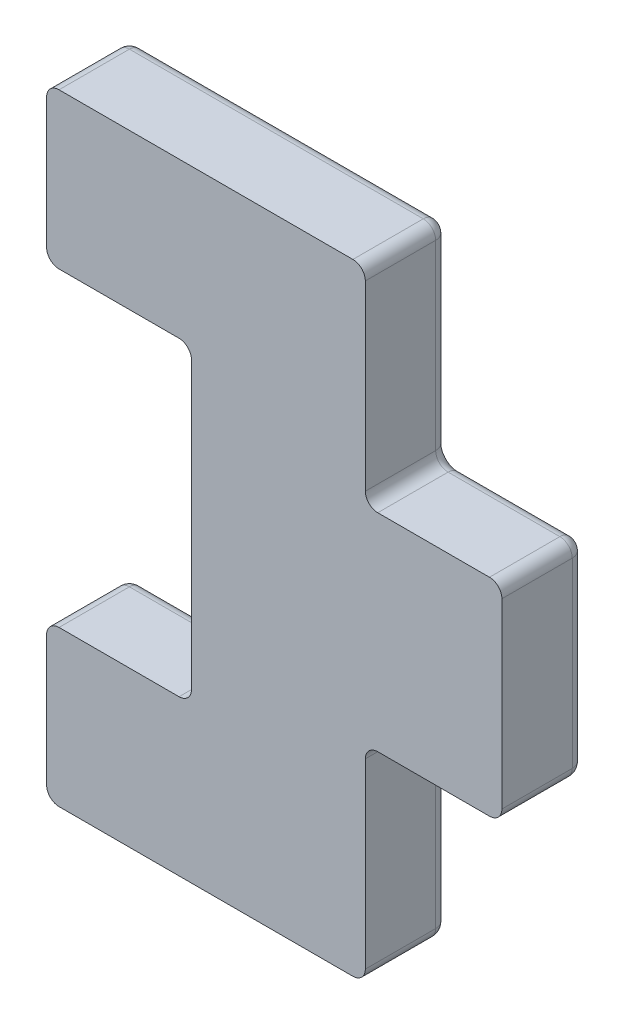
SolidWorks part; units mm, degrees
ref_plane "Ebene vorne" through (0, 0, 0) normal (0, 0, 1) x (1, 0, 0)
ref_plane "Ebene oben" through (0, 0, 0) normal (0, 1, 0) x (1, 0, 0)
ref_plane "Ebene rechts" through (0, 0, 0) normal (1, 0, 0) x (0, 0, -1)
sketch "Skizze1" plane through (0, 0, 0) normal (0, 0, 1) x (1, 0, 0)
  line L0 (0, 0) -> (7.5, 0) construction
  line L1 (0, -3.75) -> (0, 3.75)
  line L2 (0, 3.75) -> (-3.5, 3.75)
  line L3 (-3.5, 3.75) -> (-3.5, 7.5)
  line L4 (-3.5, 7.5) -> (4.2, 7.5)
  line L5 (4.2, 7.5) -> (4.2, 2.5)
  line L6 (4.2, 2.5) -> (7.5, 2.5)
  line L7 (7.5, 2.5) -> (7.5, -2.5)
  line L8 (4.2, -2.5) -> (7.5, -2.5)
  line L9 (4.2, -7.5) -> (4.2, -2.5)
  line L10 (-3.5, -7.5) -> (4.2, -7.5)
  line L11 (-3.5, -3.75) -> (-3.5, -7.5)
  line L12 (0, -3.75) -> (-3.5, -3.75)
  dimension "D1" = 15
  dimension "D2" = 7.5
  dimension "D3" = 5
  dimension "D4" = 11
  dimension "D5" = 7.7
  dimension "D6" = 3.5
extrude "Grundkörper" add sketch "Skizze1" along normal blind 2
fillet "Verrundung1" radius 0.3 12 edges at (4.2, 7.5, 1) (4.2, 2.5, 1) (7.5, 2.5, 1) (-3.5, 7.5, 1) (-3.5, 3.75, 1) (0, 3.75, 1) (0, -3.75, 1) (-3.5, -3.75, 1) (-3.5, -7.5, 1) (4.2, -7.5, 1) (4.2, -2.5, 1) (7.5, -2.5, 1)
fillet "Verrundung2" radius 0.3 24 edges at (-3.4121, 7.4121, 0) (-3.5, 5.625, 0) (-3.4121, 3.8379, 0) (-1.75, 3.75, 0) (-0.0879, 3.6621, 0) (0, 0, 0) (-0.0879, -3.6621, 0) (-1.75, -3.75, 0) (-3.4121, -3.8379, 0) (-3.5, -5.625, 0) (-3.4121, -7.4121, 0) (0.35, -7.5, 0) (4.1121, -7.4121, 0) (4.2, -5, 0) (4.2879, -2.5879, 0) (5.85, -2.5, 0) (7.4121, -2.4121, 0) (7.5, 0, 0) (7.4121, 2.4121, 0) (5.85, 2.5, 0) (4.2879, 2.5879, 0) (4.2, 5, 0) (4.1121, 7.4121, 0) (0.35, 7.5, 0)
